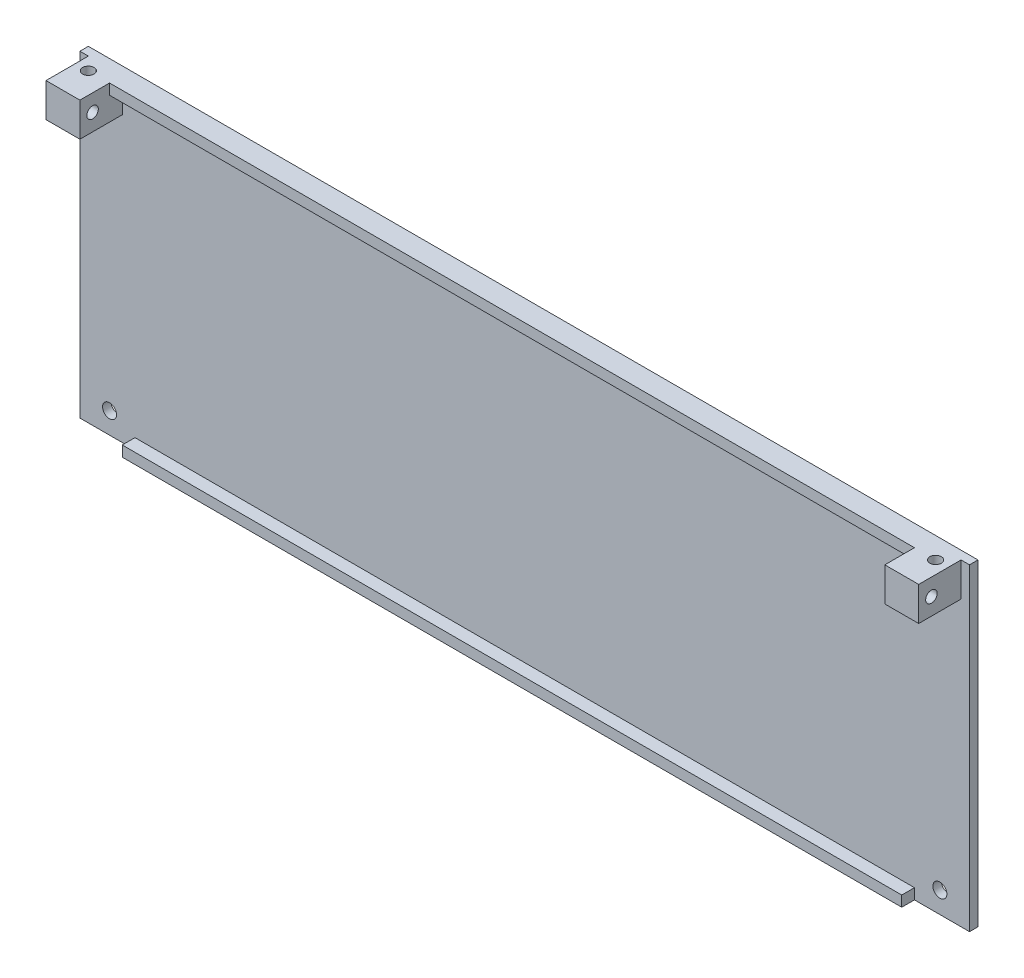
SolidWorks part; units mm, degrees
ref_plane "Front Plane" through (0, 0, 0) normal (0, 0, 1) x (1, 0, 0)
ref_plane "Top Plane" through (0, 0, 0) normal (0, 1, 0) x (1, 0, 0)
ref_plane "Right Plane" through (0, 0, 0) normal (1, 0, 0) x (0, 0, -1)
sketch "Sketch1" plane through (0, 0, 0) normal (0, 0, 1) x (1, 0, 0)
  line L0 (0, 0) -> (0, -50.4629) construction
  line L1 (-105, 37.5) -> (105, 37.5)
  line L2 (-105, 37.5) -> (-105, -37.5)
  line L3 (-105, -37.5) -> (105, -37.5)
  line L4 (105, 37.5) -> (105, -37.5)
  line L5 (-105, 37.5) -> (105, -37.5) construction
  line L6 (-105, -37.5) -> (105, 37.5) construction
  circle A0 centre (-98, -32.5) radius 1.65
  circle A1 centre (98, -32.5) radius 1.65
  point P0 (0, 0)
  dimension "D3" = 5
  dimension "D1" = 210
  dimension "D2" = 75
  dimension "D4" = 7
extrude "Boss-Extrude1" add sketch "Sketch1" along normal blind 2
sketch "Sketch2" plane through (0, 0, 2) normal (0, 0, 1) x (1, 0, 0)
  line L0 (105, 37.5) -> (-105, 37.5) construction
  line L1 (-103, 37.5) -> (-95, 37.5)
  line L2 (-103, 37.5) -> (-103, 29.5)
  line L3 (-103, 29.5) -> (-95, 29.5)
  line L4 (-95, 37.5) -> (-95, 29.5)
  line L5 (-105, 37.5) -> (-105, -37.5) construction
  line L6 (0, 0) -> (0, 66.5699) construction
  line L7 (103, 29.5) -> (95, 29.5)
  line L8 (95, 37.5) -> (95, 29.5)
  line L9 (103, 37.5) -> (95, 37.5)
  line L10 (103, 37.5) -> (103, 29.5)
  dimension "D1" = 2
  dimension "D2" = 8
  dimension "D3" = 8
extrude "Boss-Extrude2" add sketch "Sketch2" along normal blind 10
sketch "Sketch3" plane through (0, 37.5, 0) normal (0, 1, 0) x (1, 0, 0)
  line L0 (105, 0) -> (-105, 0) construction
  line L1 (-105, -2) -> (-105, 0) construction
  line L2 (0, 0) -> (0, 34.4508) construction
  circle A0 centre (-100, -5) radius 1.35
  circle A1 centre (100, -5) radius 1.35
  dimension "D1" = 5
  dimension "D2" = 5
extrude "Cut-Extrude1" cut sketch "Sketch3" against normal blind 10
sketch "Sketch4" plane through (0, 0, 2) normal (0, 0, 1) x (1, 0, 0)
  line L0 (95, 37.5) -> (-95, 37.5)
  line L1 (-95, 37.5) -> (-95, 35)
  line L2 (-95, 29.5) -> (-95, 37.5) construction
  line L3 (-95, 35) -> (95, 35)
  line L4 (95, 37.5) -> (95, 29.5) construction
  line L5 (95, 35) -> (95, 37.5)
  dimension "D1" = 2.5
extrude "Boss-Extrude3" add sketch "Sketch4" along normal blind 3
sketch "Sketch5" plane through (0, 0, 2) normal (0, 0, 1) x (1, 0, 0)
  line L0 (0, 0) -> (0, -70.2579) construction
  line L1 (-105, -37.5) -> (105, -37.5) construction
  line L2 (-92, -37.5) -> (92, -37.5)
  line L3 (-92, -37.5) -> (-92, -35)
  line L4 (-92, -35) -> (92, -35)
  line L5 (92, -37.5) -> (92, -35)
  dimension "D1" = 2.5
  dimension "D2" = 92
  dimension "D3" = 92
extrude "Boss-Extrude4" add sketch "Sketch5" along normal blind 3
sketch "Sketch6" plane through (103, 0, 0) normal (1, 0, 0) x (0, 0, -1)
  line L0 (-2, 29.5) -> (-2, 37.5) construction
  line L3 (-12, 37.5) -> (-2, 37.5) construction
  circle A0 centre (-9, 33.5) radius 1.35
  dimension "D1" = 7
  dimension "D2" = 4
extrude "Cut-Extrude2" cut sketch "Sketch6" against normal through all
